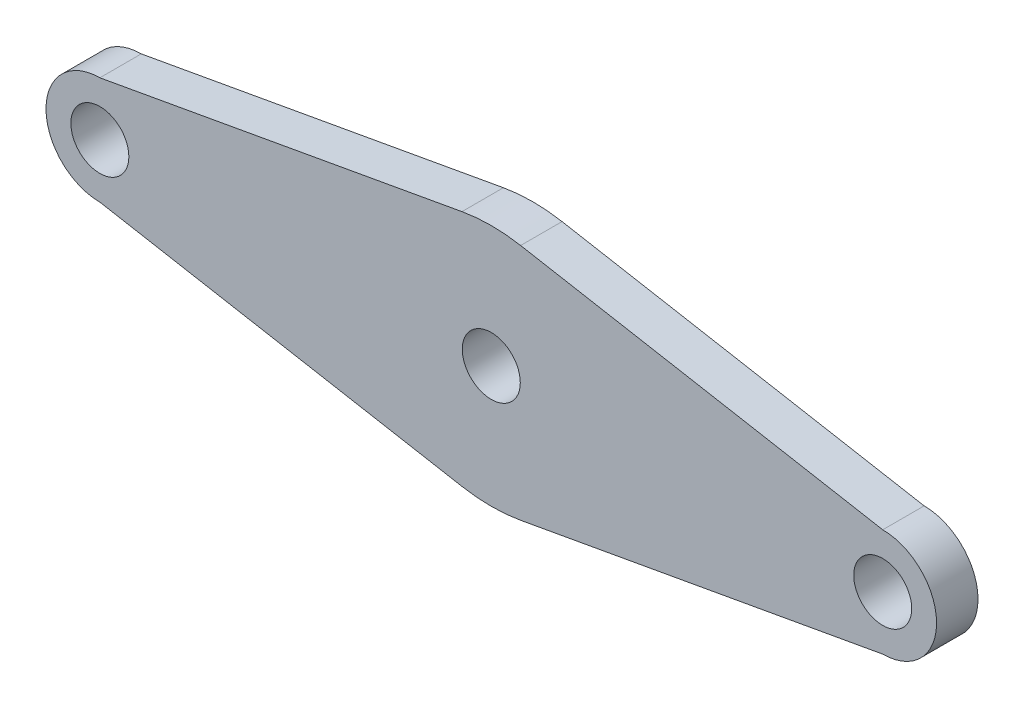
SolidWorks part; units mm, degrees
ref_plane "Front Plane" through (0, 0, 0) normal (0, 0, 1) x (1, 0, 0)
ref_plane "Top Plane" through (0, 0, 0) normal (0, 1, 0) x (1, 0, 0)
ref_plane "Right Plane" through (0, 0, 0) normal (1, 0, 0) x (0, 0, -1)
sketch "Sketch1" plane through (0, 0, 0) normal (0, 0, 1) x (1, 0, 0)
  line L0 (-23.625, 0) -> (23.625, 0)
  line L3 (0, 7.5) -> (0, -7.5) construction
  line L6 (0, 7.5) -> (-23.625, 3.25)
  line L7 (-23.625, -3.25) -> (0, -7.5)
  line L8 (0, -7.5) -> (23.625, -3.25)
  line L9 (0, 7.5) -> (23.625, 3.25)
  circle A0 centre (-23.625, 0) radius 1.75
  circle A1 centre (23.625, 0) radius 1.75
  circle A2 centre (0, 0) radius 1.75
  circle A3 centre (0, 0) radius 7.5
  circle A8 centre (-23.625, 0) radius 3.25
  circle A9 centre (23.625, 0) radius 3.25
  point P4 (0, 0)
  dimension "D1" = 3.5
  dimension "D3" = 15
  dimension "D4" = 1.5
  dimension "D2" = 23.625
extrude "Boss-Extrude1" add sketch "Sketch1" along normal blind 2.5
fillet "Fillet1" radius 10 2 edges at (0, -7.5, 1.25) (0, 7.5, 1.25)
